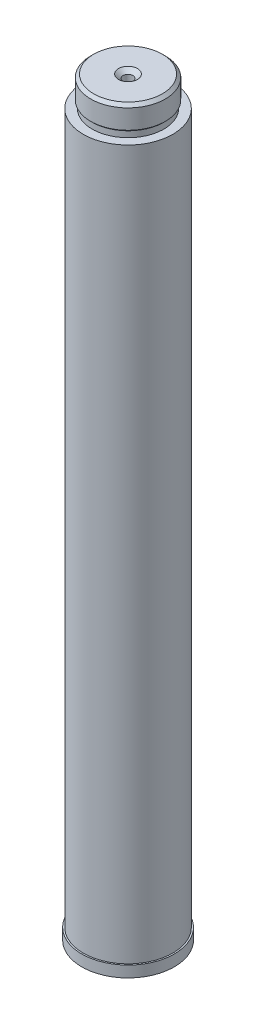
SolidWorks part; units mm, degrees
ref_plane "Front Plane" through (0, 0, 0) normal (0, 0, 1) x (1, 0, 0)
ref_plane "Top Plane" through (0, 0, 0) normal (0, 1, 0) x (1, 0, 0)
ref_plane "Right Plane" through (0, 0, 0) normal (1, 0, 0) x (0, 0, -1)
sketch "Sketch1" plane through (0, 0, 0) normal (0, 1, 0) x (1, 0, 0)
  circle A0 centre (0, 0) radius 39.37
  dimension "D1" = 78.74
extrude "Boss-Extrude1" add sketch "Sketch1" along normal blind 9.525
sketch "Sketch2" plane through (0, 9.525, 0) normal (0, 1, 0) x (1, 0, 0)
  circle A0 centre (0, 0) radius 38.1
  dimension "D1" = 76.2
extrude "Boss-Extrude2" add sketch "Sketch2" along normal blind 603.25
shell "Shell1" thickness 2.54
sketch "Sketch4" plane through (0, 0, 0) normal (0, 0, 1) x (1, 0, 0)
  line L0 (0, 0) -> (0, 50000) construction
  line L1 (0, 612.775) -> (30.48, 612.775)
  line L2 (38.1, 612.775) -> (-38.1, 612.775) construction
  line L3 (30.48, 612.775) -> (30.48, 617.855)
  line L4 (30.48, 617.855) -> (31.75, 619.125)
  line L5 (31.75, 619.125) -> (31.75, 635.635)
  line L6 (29.21, 638.175) -> (0, 638.175)
  line L7 (0, 638.175) -> (0, 612.775)
  line L8 (31.75, 635.635) -> (29.21, 638.175)
  line L9 (39.37, 9.525) -> (-39.37, 9.525) construction
  point P9 (31.75, 638.175)
  dimension "D1" = 31.75
  dimension "D2" = 30.48
  dimension "D3" = 135
  dimension "D4" = 5.08
  dimension "D5" = 628.65
revolve "Revolve1" add sketch "Sketch4" angle 360 about L0
hole_wizard "CSK for 5/16 Flat Head Machine Screw (100)1" positions "Sketch5" profile "Sketch6" countersink size "5/16" standard "ANSI Inch"
sketch "Sketch5" plane through (0, 638.175, 0) normal (0, 1, 0) x (1, 0, 0)
  point P0 (0, 0)
sketch "Sketch6" plane through (0, 638.175, 0) normal (1, 0, 0) x (0, 0, 1)
  line L0 (0, 0) -> (0, 15.2335)
  line L1 (0, 15.2335) -> (4.2164, 12.7)
  line L2 (4.2164, 12.7) -> (4.2164, 3.2289)
  line L3 (4.2164, 3.2289) -> (8.0645, 0)
  line L5 (8.0645, 0) -> (0, 0)
  line L6 (-4.2164, 3.2289) -> (-8.0645, 0) construction
  line L10 (0, 15.2335) -> (-4.2164, 12.7) construction
  line L11 (0, -6.35) -> (0, 107.95) construction
  dimension "Hole Dia." = 8.4328
  dimension "Hole Depth" = 12.7
  dimension "Near C'Sink Dia." = 16.129
  dimension "Near C'Sink Angle" = 100
  dimension "Drill Angle" = 118
